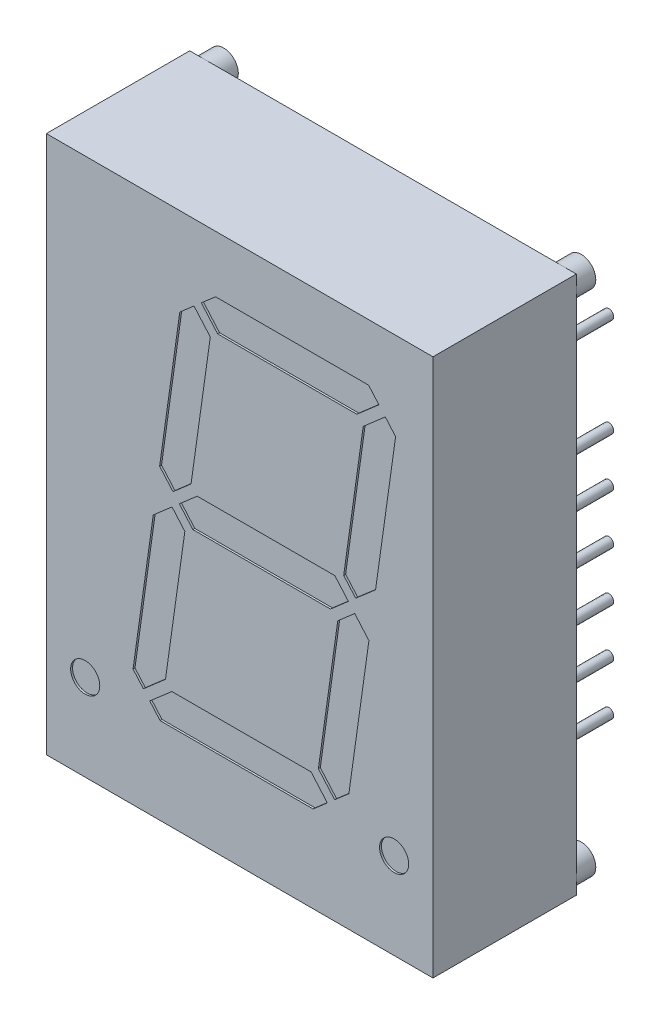
SolidWorks part; units mm, degrees
ref_plane "Спереди" through (0, 0, 0) normal (0, 0, 1) x (1, 0, 0)
ref_plane "Сверху" through (0, 0, 0) normal (0, 1, 0) x (1, 0, 0)
ref_plane "Справа" through (0, 0, 0) normal (1, 0, 0) x (0, 0, -1)
sketch "Эскиз1" plane through (0, 0, 0) normal (0, 0, 1) x (1, 0, 0)
  line L1 (-9.95, -13.845) -> (9.95, -13.845)
  line L2 (-9.95, -13.845) -> (-9.95, 13.845)
  line L3 (-9.95, 13.845) -> (9.95, 13.845)
  line L4 (9.95, -13.845) -> (9.95, 13.845)
  line L5 (-9.95, -13.845) -> (9.95, 13.845) construction
  line L6 (-9.95, 13.845) -> (9.95, -13.845) construction
  point P0 (0, 0)
  dimension "D1" = 19.9
  dimension "D2" = 27.69
extrude "Бобышка-Вытянуть1" add sketch "Эскиз1" along normal blind 7.38 from offset 1
sketch "Эскиз3" plane through (0, 0, 1) normal (0, 0, -1) x (-1, 0, 0)
  line L0 (-9.95, 13.845) -> (9.95, 13.845) construction
  line L1 (-9.95, -13.845) -> (-9.95, 13.845) construction
  line L2 (9.95, 13.845) -> (9.95, -13.845) construction
  line L3 (9.95, -13.845) -> (-9.95, -13.845) construction
  circle A0 centre (-9.2, 13.095) radius 0.75
  circle A1 centre (9.2, 13.095) radius 0.75
  circle A2 centre (9.2, -13.095) radius 0.75
  circle A3 centre (-9.2, -13.095) radius 0.75
  dimension "D1" = 1.5
extrude "Бобышка-Вытянуть3" add sketch "Эскиз3" along normal blind 1
sketch "Эскиз2" plane through (0, 0, 1) normal (0, 0, -1) x (-1, 0, 0)
  line L0 (-7.62, 0) -> (7.62, 0) construction
  line L1 (7.62, 12.8466) -> (7.62, -16.0698) construction
  line L2 (-7.62, 16.0533) -> (-7.62, -15.5466) construction
  circle A0 centre (-7.62, -8.89) radius 0.25
  circle A1 centre (7.62, -8.89) radius 0.25 [skipped]
  circle A2 centre (7.62, -6.35) radius 0.25 [skipped]
  circle A3 centre (7.62, -3.81) radius 0.25
  circle A4 centre (7.62, -1.27) radius 0.25
  circle A5 centre (7.62, 1.27) radius 0.25
  circle A6 centre (7.62, 3.81) radius 0.25
  circle A7 centre (7.62, 6.35) radius 0.25
  circle A8 centre (7.62, 8.89) radius 0.25
  circle A9 centre (-7.62, -6.35) radius 0.25
  circle A10 centre (-7.62, -3.81) radius 0.25
  circle A11 centre (-7.62, -1.27) radius 0.25
  circle A12 centre (-7.62, 1.27) radius 0.25
  circle A13 centre (-7.62, 3.81) radius 0.25
  circle A14 centre (-7.62, 6.35) radius 0.25 [skipped]
  circle A15 centre (-7.62, 8.89) radius 0.25
  point P4 (0, 0)
  dimension "D3" = 0.5
  dimension "D1" = 15.24
  dimension "D2" = 8.89
  dimension "D4" = 2
  dimension "D5" = 8
extrude "Бобышка-Вытянуть2" add sketch "Эскиз2" along normal blind 4
sketch "Эскиз4" plane through (0, 0, 8.38) normal (0, 0, 1) x (1, 0, 0)
  line L0 (-5.7119, -9.395) -> (5.3962, -9.395) construction
  line L1 (-2.8562, 10.925) -> (8.2519, 10.925) construction
  line L2 (-9.95, -13.845) -> (9.95, -13.845) construction
  line L3 (-2.8562, 10.925) -> (-5.7119, -9.395) construction
  line L4 (8.2519, 10.925) -> (5.3962, -9.395) construction
  line L5 (1.27, -9.395) -> (1.27, 10.925) construction
  line L6 (-4.2841, 0.765) -> (6.8241, 0.765) construction
  line L7 (-3.1045, 0.765) -> (-2.1842, 1.565)
  line L8 (9.95, -13.845) -> (9.95, 13.845) construction
  line L9 (-4.0962, -9.395) -> (3.7804, -9.395)
  line L10 (3.7804, -9.395) -> (4.512, -8.759)
  line L11 (4.512, -8.759) -> (3.674, -7.795)
  line L12 (3.674, -7.795) -> (-3.4903, -7.795)
  line L13 (-3.4903, -7.795) -> (-4.6276, -8.7837)
  line L14 (-4.6276, -8.7837) -> (-4.0962, -9.395)
  line L15 (5.0485, -0.3724) -> (4.0514, -7.467)
  line L16 (4.0514, -7.467) -> (4.8894, -8.431)
  line L17 (4.8894, -8.431) -> (5.621, -7.795)
  line L18 (5.621, -7.795) -> (6.653, -0.4524)
  line L19 (6.653, -0.4524) -> (5.9228, 0.3876)
  line L20 (5.9228, 0.3876) -> (5.0485, -0.3724)
  line L21 (-2.1842, 1.565) -> (4.8993, 1.565)
  line L22 (4.8993, 1.565) -> (5.5947, 0.765)
  line L23 (5.5947, 0.765) -> (4.6744, -0.035)
  line L24 (4.6744, -0.035) -> (-2.4091, -0.035)
  line L25 (-2.4091, -0.035) -> (-3.1045, 0.765)
  line L26 (-4.1199, 1.933) -> (-3.4326, 1.1424)
  line L27 (-3.4326, 1.1424) -> (-2.5016, 1.9517)
  line L28 (-4.4482, -0.403) -> (-3.4819, 0.437)
  line L29 (-3.4819, 0.437) -> (-2.8212, -0.323)
  line L30 (-2.8212, -0.323) -> (-3.8183, -7.4176)
  line L31 (-3.8183, -7.4176) -> (-4.9557, -8.4063)
  line L32 (-4.9557, -8.4063) -> (-5.4871, -7.795)
  line L33 (-5.4871, -7.795) -> (-4.4482, -0.403)
  line L34 (-2.5016, 1.9517) -> (-1.5114, 8.997)
  line L35 (-1.5114, 8.997) -> (-2.3494, 9.961)
  line L36 (-2.3494, 9.961) -> (-3.081, 9.325)
  line L37 (-3.081, 9.325) -> (-4.1199, 1.933)
  line L38 (-1.2404, 10.925) -> (-1.972, 10.289)
  line L39 (-1.972, 10.289) -> (-1.134, 9.325)
  line L40 (-1.134, 9.325) -> (6.0303, 9.325)
  line L41 (6.0303, 9.325) -> (7.1676, 10.3137)
  line L42 (7.1676, 10.3137) -> (6.6362, 10.925)
  line L43 (6.6362, 10.925) -> (-1.2404, 10.925)
  line L44 (6.3583, 8.9476) -> (7.4957, 9.9363)
  line L45 (7.4957, 9.9363) -> (8.0271, 9.325)
  line L46 (8.0271, 9.325) -> (6.9951, 1.9824)
  line L47 (6.9951, 1.9824) -> (5.9721, 1.093)
  line L48 (5.9721, 1.093) -> (5.3543, 1.8037)
  line L49 (5.3543, 1.8037) -> (6.3583, 8.9476)
  line L50 (-9.95, 13.845) -> (-9.95, -13.845) construction
  circle A0 centre (-7.95, -9.395) radius 0.75
  circle A1 centre (7.95, -9.395) radius 0.75
  point P14 (1.27, 0.765)
  point P61 (0, 0)
  point P62 (0, 0)
  dimension "D25" = 1.5
  dimension "D1" = 20.32
  dimension "D2" = 4.45
  dimension "D3" = 82
  dimension "D4" = 11
  dimension "D5" = 8.68
  dimension "D6" = 1.6
  dimension "D7" = 0.8
  dimension "D8" = 49
  dimension "D9" = 0.25
  dimension "D10" = 1.6
  dimension "D11" = 1.6
  dimension "D12" = 0.25
  dimension "D13" = 41
  dimension "D14" = 0.25
  dimension "D15" = 1.6
  dimension "D16" = 0.25
  dimension "D17" = 0.5
  dimension "D18" = 0.25
  dimension "D19" = 1.6
  dimension "D20" = 0.25
  dimension "D21" = 0.5
  dimension "D22" = 0.25
  dimension "D23" = 0.25
  dimension "D24" = 2
  dimension "D26" = 2
extrude "Вырез-Вытянуть1" cut sketch "Эскиз4" against normal blind 0.1
